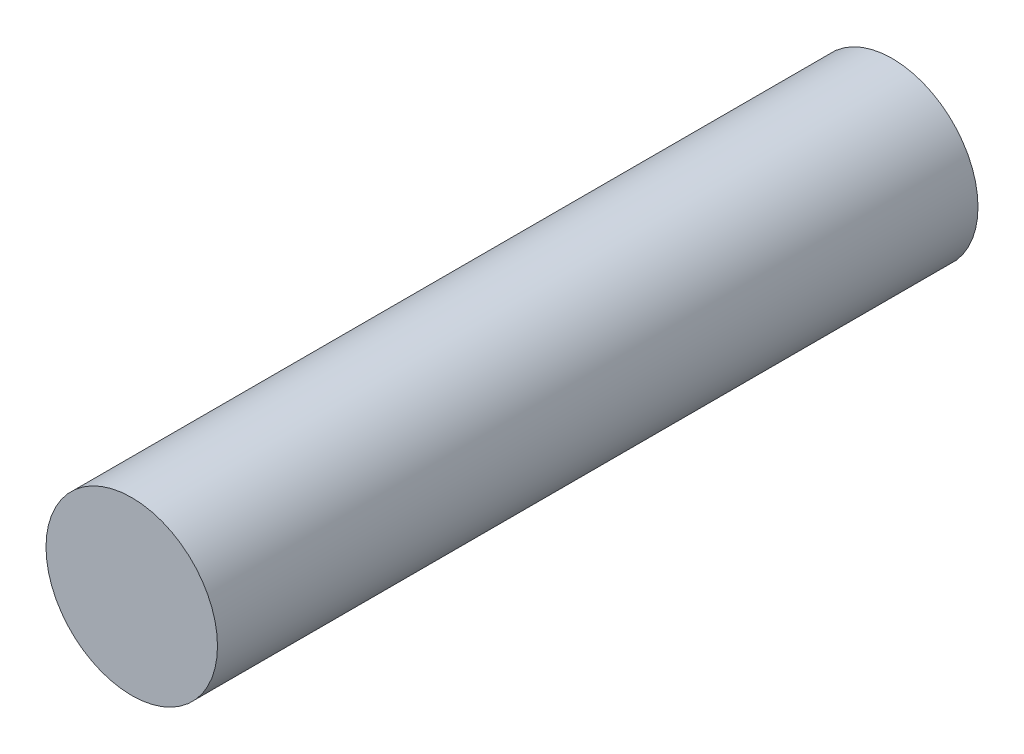
SolidWorks part; units mm, degrees
ref_plane "Front" through (0, 0, 0) normal (0, 0, 1) x (1, 0, 0)
ref_plane "Top" through (0, 0, 0) normal (0, 1, 0) x (1, 0, 0)
ref_plane "Right" through (0, 0, 0) normal (1, 0, 0) x (0, 0, -1)
sketch "Sketch1" plane through (0, 0, 0) normal (0, 0, 1) x (1, 0, 0)
  circle A0 centre (0, 0) radius 9.0195
  dimension "D1" = 18.039
extrude "Boss-Extrude1" add sketch "Sketch1" against normal blind 80
